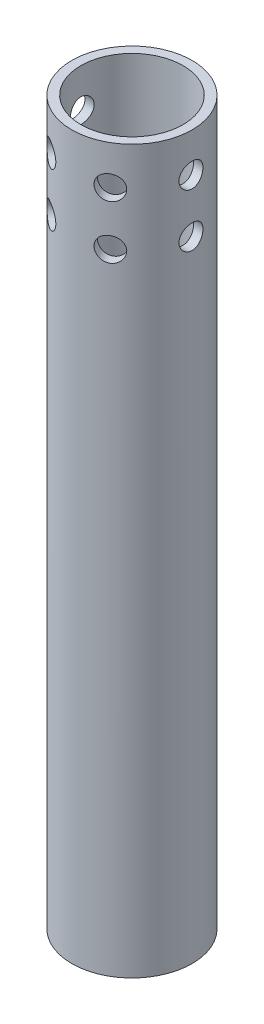
SolidWorks part; units mm, degrees
ref_plane "Front Plane" through (0, 0, 0) normal (0, 0, 1) x (1, 0, 0)
ref_plane "Top Plane" through (0, 0, 0) normal (0, 1, 0) x (1, 0, 0)
ref_plane "Right Plane" through (0, 0, 0) normal (1, 0, 0) x (0, 0, -1)
sketch "Sketch1" plane through (0, 0, 0) normal (0, 1, 0) x (1, 0, 0)
  circle A0 centre (0, 0) radius 9.525
  dimension "D1" = 19.05
extrude "Boss-Extrude1" add sketch "Sketch1" along normal blind 114.3
sketch "Sketch2" plane through (0, 114.3, 0) normal (0, 1, 0) x (1, 0, 0)
  circle A0 centre (0, 0) radius 8.0956
extrude "Cut-Extrude1" cut sketch "Sketch2" against normal blind 107.95 and the other way through all
sketch "Sketch4" plane through (0, 0, 0) normal (1, 0, 0) x (0, 0, -1)
  circle A0 centre (0, 108.1191) radius 1.8987
  dimension "D1" = 3.7973
extrude "Cut-Extrude2" cut sketch "Sketch4" along normal blind 114.3
pattern_circular "CirPattern1" count 4 every 60 about axis through (0, 114.3, 0) along (0, -1, 0) of "Cut-Extrude2"
pattern_linear "LPattern1" count 2 spacing 8.4582 along (0, -1, 0) of "CirPattern1", "Cut-Extrude2"
sketch "Sketch5" plane through (0, 0, 0) normal (0, -1, 0) x (1, 0, 0)
  circle A0 centre (0, 0) radius 2.921
  dimension "D1" = 5.842
extrude "Cut-Extrude3" cut sketch "Sketch5" against normal blind 114.3
